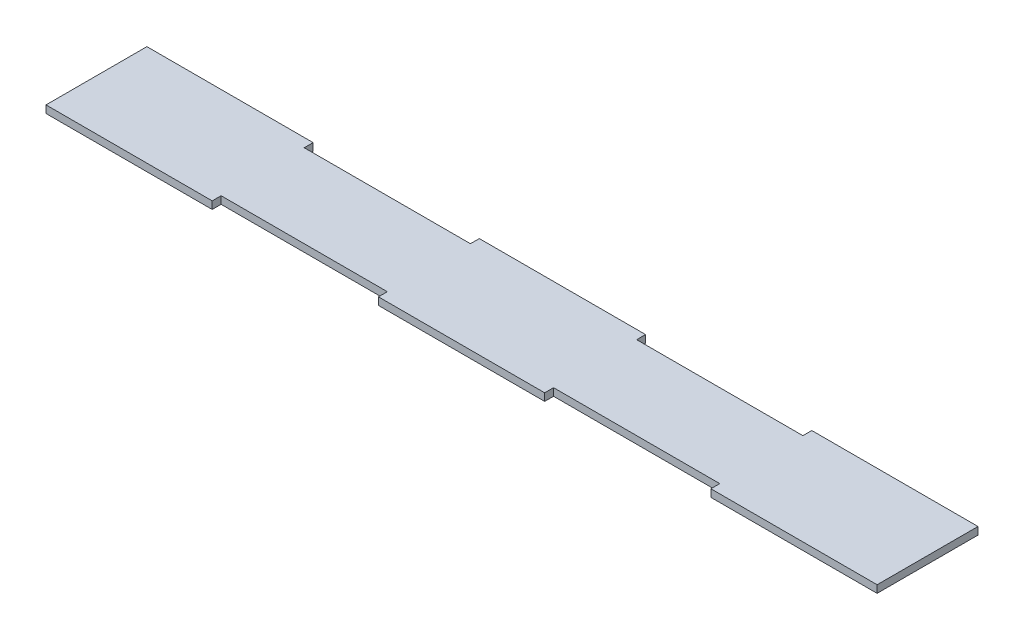
SolidWorks part; units mm, degrees
ref_plane "Front Plane" through (0, 0, 0) normal (0, 0, 1) x (1, 0, 0)
ref_plane "Top Plane" through (0, 0, 0) normal (0, 1, 0) x (1, 0, 0)
ref_plane "Right Plane" through (0, 0, 0) normal (1, 0, 0) x (0, 0, -1)
sketch "Sketch1" plane through (0, 0, 0) normal (0, 1, 0) x (1, 0, 0)
  line L0 (30, 15) -> (90, 15)
  line L1 (-150, 18.21) -> (-90, 18.21)
  line L5 (-90, 15) -> (-30, 15)
  line L7 (-30, 18.21) -> (30, 18.21)
  line L9 (90, 18.21) -> (150, 18.21)
  line L14 (-90, 18.21) -> (-90, 15)
  line L15 (-30, 18.21) -> (-30, 15)
  line L16 (30, 18.21) -> (30, 15)
  line L17 (90, 18.21) -> (90, 15)
  line L19 (90, -18.21) -> (150, -18.21)
  line L20 (90, -18.21) -> (90, -15)
  line L21 (30, -15) -> (90, -15)
  line L22 (30, -18.21) -> (30, -15)
  line L23 (-30, -18.21) -> (-30, -15)
  line L24 (-30, -18.21) -> (30, -18.21)
  line L25 (-90, -15) -> (-30, -15)
  line L26 (-150, -18.21) -> (-90, -18.21)
  line L27 (-90, -15) -> (-90, -18.21)
  line L28 (-150, 18.21) -> (-150, -18.21)
  line L29 (150, 18.21) -> (150, -18.21)
  point P0 (0, 0)
  dimension "D1" = 300
  dimension "D4" = 3.21
extrude "Boss-Extrude1" add sketch "Sketch1" along normal blind 2.7
